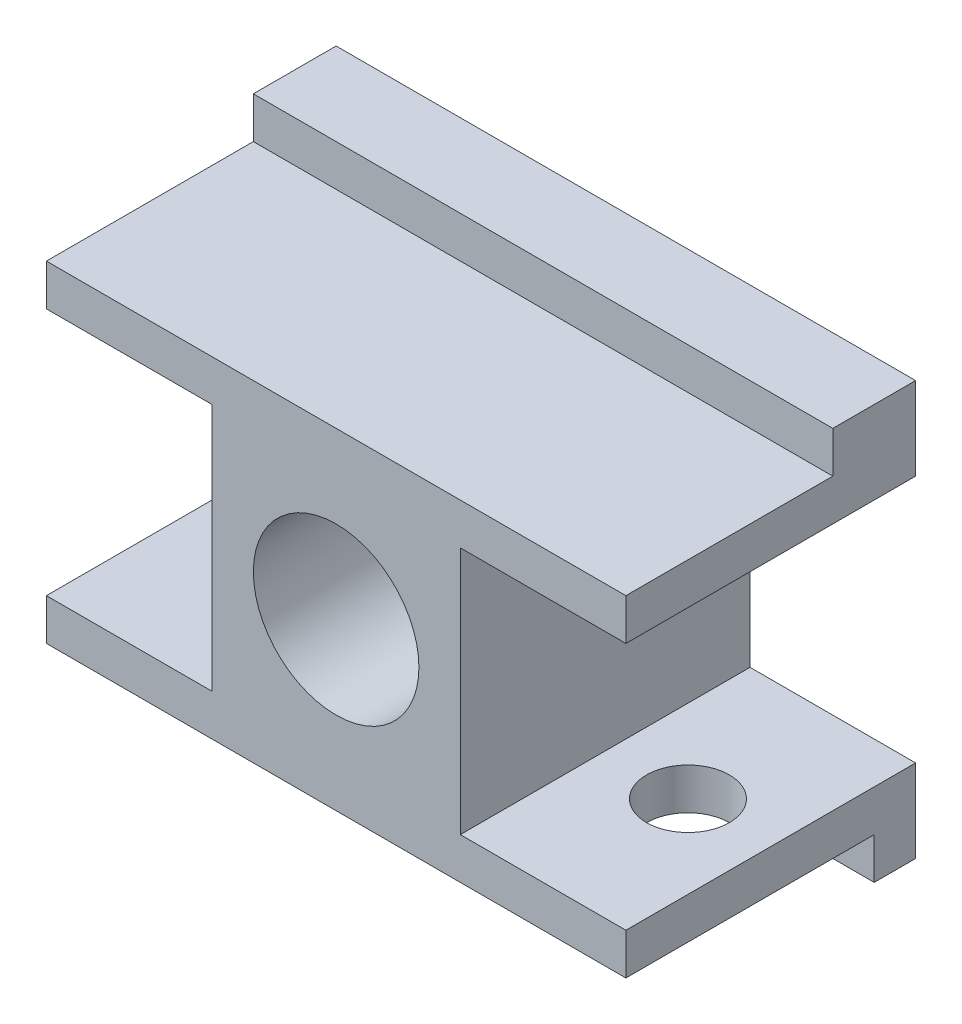
SolidWorks part; units mm, degrees
ref_plane "Front Plane" through (0, 0, 0) normal (0, 0, 1) x (1, 0, 0)
ref_plane "Top Plane" through (0, 0, 0) normal (0, 1, 0) x (1, 0, 0)
ref_plane "Right Plane" through (0, 0, 0) normal (1, 0, 0) x (0, 0, -1)
sketch "Sketch1" plane through (0, 0, 0) normal (0, 1, 0) x (1, 0, 0)
  line L0 (0, 0) -> (0, 5)
  line L1 (0, 5) -> (70, 5)
  line L2 (70, 5) -> (70, 0)
  line L3 (70, 0) -> (0, 0)
  dimension "D1" = 5
  dimension "D2" = 70
extrude "Boss-Extrude1" add sketch "Sketch1" along normal blind 10
sketch "Sketch2" plane through (0, 0, 0) normal (0, 0, 1) x (1, 0, 0)
  line L0 (0, 10) -> (0, 5)
  line L1 (0, 10) -> (0, 0) construction
  line L2 (0, 5) -> (70, 5)
  line L3 (70, 10) -> (70, 0) construction
  line L4 (70, 5) -> (70, 10)
  line L5 (70, 10) -> (0, 10)
extrude "Boss-Extrude2" add sketch "Sketch2" along normal blind 30
sketch "Sketch3" plane through (0, 0, 0) normal (0, 1, 0) x (1, 0, 0)
  line L0 (70, -30) -> (70, 5) construction
  line L2 (70, 5) -> (0, 5) construction
  circle A0 centre (60, -12.5) radius 5
  point P3 (70, -12.5)
  dimension "D2" = 10
  dimension "D1" = 10
  dimension "D3" = 17.5
extrude "Cut-Extrude2" cut sketch "Sketch3" along normal blind 10 contours A0
sketch "Sketch4" plane through (0, 0, 0) normal (0, 1, 0) x (1, 0, 0)
  line L0 (0, 5) -> (0, -30) construction
  line L3 (70, 5) -> (0, 5) construction
  circle A0 centre (10, -12.5) radius 5
  point P6 (10.0519, 5)
  dimension "D2" = 10
  dimension "D1" = 10
  dimension "D3" = 17.5
extrude "Cut-Extrude3" cut sketch "Sketch4" along normal blind 10 contours A0
sketch "Sketch6" plane through (0, 10, 0) normal (0, 1, 0) x (1, 0, 0)
  line L0 (70, 5) -> (50, 5)
  line L1 (70, 5) -> (0, 5) construction
  line L2 (50, 5) -> (20, 5)
  line L3 (20, 5) -> (20, -30)
  line L4 (70, -30) -> (0, -30) construction
  line L5 (20, -30) -> (50, -30)
  line L6 (50, -30) -> (50, 5)
  line M9 (0, -30) -> (70, -30)
  line M11 (70, 5) -> (0, 5)
  dimension "D1" = 20
  dimension "D2" = 30
extrude "Boss-Extrude4" add sketch "Sketch6" along normal blind 30 contours L6 L3 M9 M11
sketch "Sketch7" plane through (0, 40, 0) normal (0, 1, 0) x (1, 0, 0)
  line L0 (20, 5) -> (0, 5)
  line L1 (0, 5) -> (0, -30)
  line L2 (0, -30) -> (70, -30)
  line L3 (70, -30) -> (70, 5)
  line L4 (70, 5) -> (20, 5)
extrude "Boss-Extrude5" add sketch "Sketch7" along normal blind 5
sketch "Sketch8" plane through (0, 45, 0) normal (0, 1, 0) x (1, 0, 0)
  line L0 (70, 5) -> (70, -5)
  line L1 (70, -30) -> (70, 5) construction
  line L2 (70, 5) -> (0, 5)
  line L3 (0, 5) -> (0, -5)
  line L4 (0, 5) -> (0, -30) construction
  line L5 (0, -5) -> (70, -5)
  dimension "D1" = 10
extrude "Boss-Extrude6" add sketch "Sketch8" along normal blind 5
sketch "Sketch9" plane through (0, 0, 30) normal (0, 0, 1) x (1, 0, 0)
  line L0 (50, 40) -> (50, 10) construction
  line L3 (0, 45) -> (70, 45) construction
  circle A0 centre (35, 25) radius 10
  point P3 (0, 0)
  point P7 (0, 0)
  dimension "D1" = 20
  dimension "D2" = 15
  dimension "D3" = 20
extrude "Cut-Extrude4" cut sketch "Sketch9" against normal blind 30 contours A0
